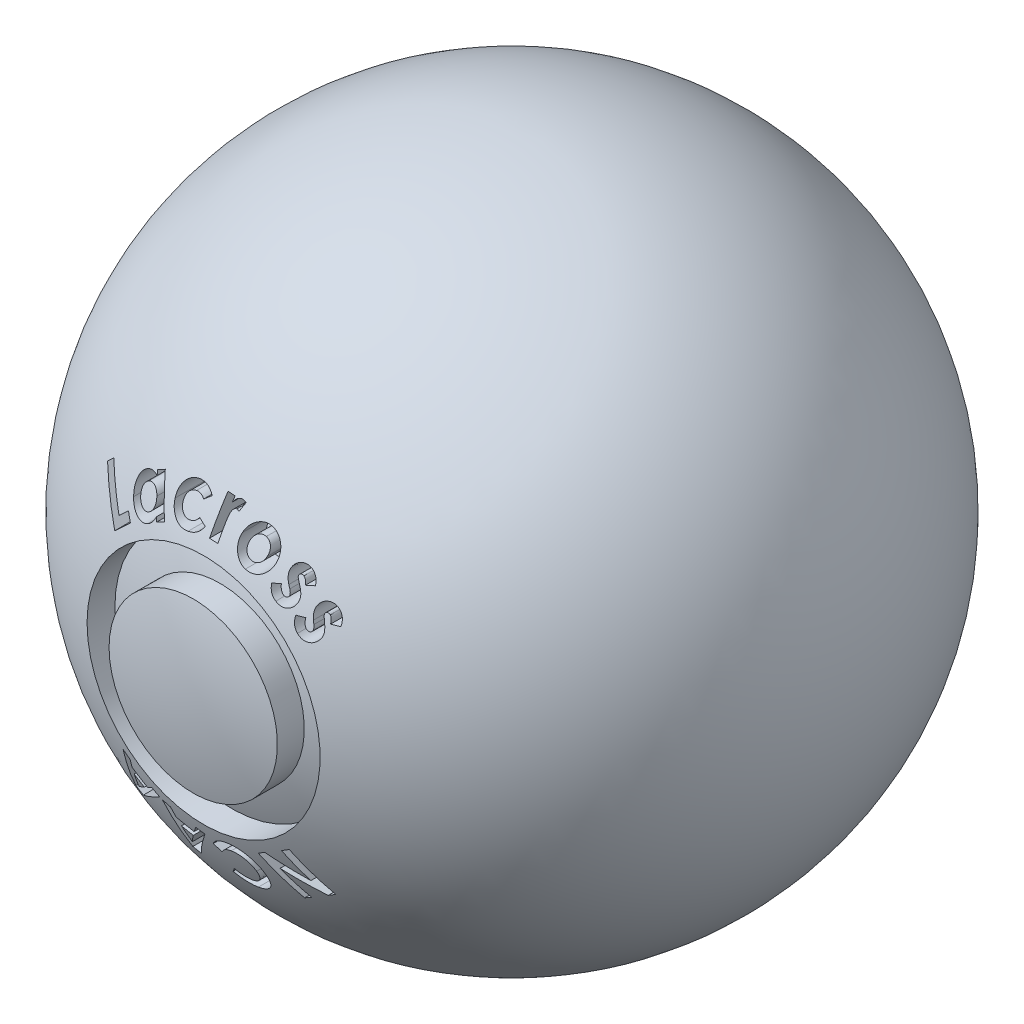
SolidWorks part; units mm, degrees
ref_plane "Front Plane" through (0, 0, 0) normal (0, 0, 1) x (1, 0, 0)
ref_plane "Top Plane" through (0, 0, 0) normal (0, 1, 0) x (1, 0, 0)
ref_plane "Right Plane" through (0, 0, 0) normal (1, 0, 0) x (0, 0, -1)
sketch "Sketch1" plane through (0, 0, 0) normal (0, 0, 1) x (1, 0, 0)
  line L0 (0, 32.3342) -> (0, -32.3342) construction
  circle A0 centre (0, 0) radius 32.3342
  dimension "D1" = 64.6684
revolve "base" add sketch "Sketch1" angle 360 about L0
ref_plane "Plane1" through (0, 0, 38.1) normal (0, 0, 1) x (1, 0, 0)
sketch "Sketch3" plane through (0, 0, 38.1) normal (0, 0, 1) x (1, 0, 0)
  line L0 (-12.7, 0) -> (0, 0) construction
  line L1 (0, 0) -> (12.7, 0) construction
  arc A0 (-12.7, 0) -> (12.7, 0) centre (0, 0) cw construction
  arc A1 (-12.7, 0) -> (12.7, 0) centre (0, 0) ccw construction
  circle A2 centre (0, 0) radius 11.43
  circle A3 centre (0, 0) radius 8.255
  text T0 "<b>Lacross</b>" font "Century Gothic" height 4.445
  text T1 "<b>NCAA</b>" font "Century Gothic" height 4.445
  dimension "D1" = 12.7
  dimension "D2" = 1.27
  dimension "D3" = 3.175
extrude "logo" cut sketch "Sketch3" against normal offset from surface (11.1368 mm away) 2.54 contours A2
